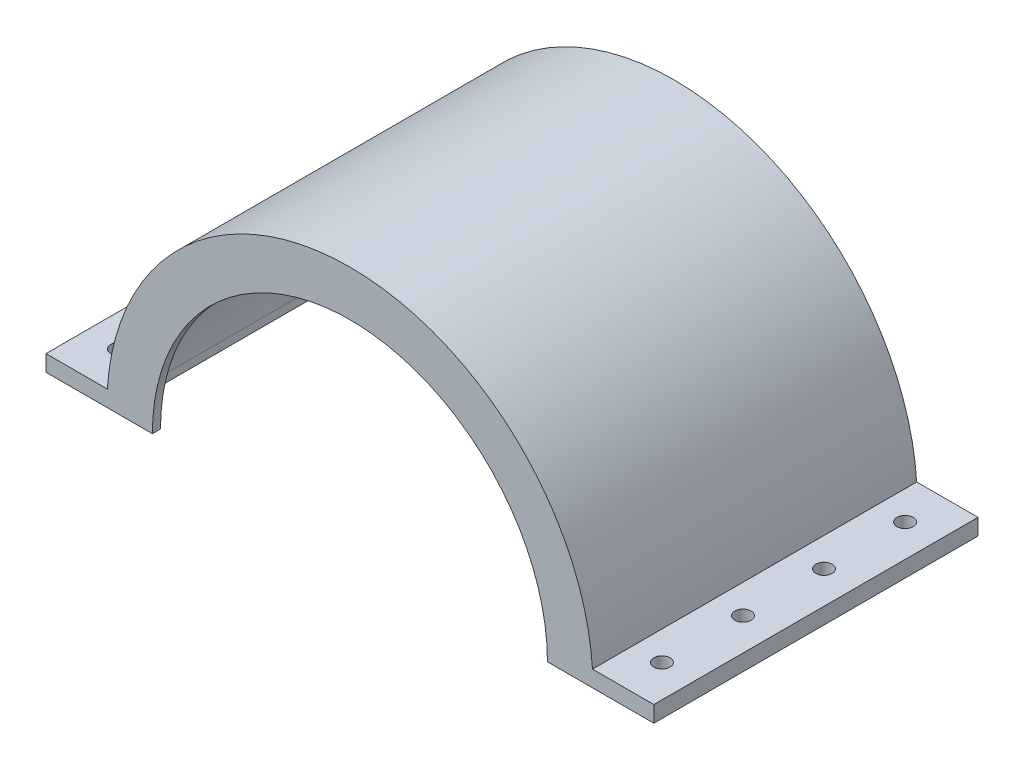
SolidWorks part; units mm, degrees
ref_plane "Front Plane" through (0, 0, 0) normal (0, 0, 1) x (1, 0, 0)
ref_plane "Top Plane" through (0, 0, 0) normal (0, 1, 0) x (1, 0, 0)
ref_plane "Right Plane" through (0, 0, 0) normal (1, 0, 0) x (0, 0, -1)
sketch "Sketch1" plane through (0, 0, 0) normal (0, 0, 1) x (1, 0, 0)
  line L0 (-75, 0) -> (75, 0)
  line L1 (0, 0) -> (0, 73.1042) construction
  line L2 (75, 0) -> (75, 4)
  line L3 (-75, 0) -> (-75, 4)
  line L4 (75, 4) -> (59.8665, 4)
  line L5 (-75, 4) -> (-59.8665, 4)
  arc A0 (59.8665, 4) -> (-59.8665, 4) centre (0, 0) ccw
  dimension "D1" = 120
  dimension "D2" = 75
  dimension "D3" = 73.1042
  dimension "D4" = 4
  dimension "D5" = 15.1335
extrude "Boss-Extrude1" add sketch "Sketch1" along normal blind 80
shell "Shell1" thickness 2
sketch "Sketch2" plane through (0, 2, 0) normal (0, -1, 0) x (1, 0, 0)
  line L1 (-73, 78) -> (-57.9655, 78)
  line L2 (-73, 78) -> (-73, 2)
  line L3 (-73, 2) -> (-57.9655, 2)
  line L4 (-57.9655, 78) -> (-57.9655, 2)
  line L5 (57.9123, 78) -> (73, 78)
  line L6 (57.9123, 78) -> (57.9123, 2)
  line L7 (57.9123, 2) -> (73, 2)
  line L8 (73, 78) -> (73, 2)
  dimension "D1" = 76
  dimension "D2" = 15.0345
  dimension "D3" = 76
  dimension "D4" = 15.0877
extrude "Boss-Extrude2" add sketch "Sketch2" along normal up to surface (2 mm away) up to face at (0, 0, 40)
sketch "Sketch3" plane through (0, 0, 80) normal (0, 0, 1) x (1, 0, 0)
  line L0 (-48.75, 0) -> (48.75, 0)
  arc A0 (48.75, 0) -> (-48.75, 0) centre (0, 0) ccw
  dimension "D2" = 97.5
extrude "Cut-Extrude1" cut sketch "Sketch3" against normal up to next
sketch "Sketch5" plane through (0, 0, 0) normal (0, 0, -1) x (-1, 0, 0)
  line L0 (-15, 0) -> (15, 0)
  arc A0 (15, 0) -> (-15, 0) centre (0, 0) ccw
  dimension "D1" = 30
  dimension "D2" = 30
extrude "Cut-Extrude2" cut sketch "Sketch5" against normal up to next
sketch "Sketch6" plane through (0, 0, 0) normal (0, -1, 0) x (1, 0, 0)
  circle A0 centre (67, 70) radius 2
  dimension "D3" = 4
  dimension "D4" = 67
  dimension "D5" = 70
extrude "Cut-Extrude6" cut sketch "Sketch6" against normal through all
pattern_linear "LPattern1" count 4 spacing 20 along (0, 0, -1) of "Cut-Extrude6"
ref_plane "Plane1" through (0, 0, 0) normal (1, 0, 0) x (0, 0, -1)
mirror "Mirror1" about plane through (0, 0, 0) normal (1, 0, 0) of "LPattern1", "Cut-Extrude6"
ref_plane "Plane2" through (-81.5, 0, 0) normal (1, 0, 0) x (0, 0, -1)
ref_plane "Plane3" through (0, 0, 40) normal (0, 0, 1) x (1, 0, 0)
sketch "Sketch7" plane through (0, 0, 40) normal (0, 0, 1) x (1, 0, 0)
  line L0 (-81.5, -45.1099) -> (-81.5, 45.1099) construction
  line L1 (-39.911, -2.6667) -> (-39.911, 97.3333) construction
  line L3 (59.8665, 4) -> (-39.911, -2.6667) construction
  line L4 (-39.911, 97.3333) -> (-81.5, 97.3333)
  arc A0 (59.8665, 4) -> (-39.911, 97.3333) centre (-39.911, -2.6667) ccw
  point P8 (-81.5, 0)
  point P9 (-81.5, 137.1762)
  dimension "D3" = 100
  dimension "D1" = 97.3333
sketch "Sketch11" plane through (-81.5, 0, 0) normal (1, 0, 0) x (0, 0, -1)
  line L0 (-225.3158, 127.91) -> (-214.0658, 106.91) construction
  line L1 (-225.3158, 127.91) -> (-202.8158, 127.91)
  line L2 (-240.3158, 112.91) -> (-240.3158, 100.91)
  line L3 (-225.3158, 85.91) -> (-202.8158, 85.91)
  line L4 (-187.8158, 112.91) -> (-187.8158, 100.91)
  line L5 (-214.0658, 106.91) -> (-202.8158, 85.91) construction
  line L6 (-225.3158, 85.91) -> (-202.8158, 127.91) construction
  arc A0 (-202.8158, 85.91) -> (-187.8158, 100.91) centre (-202.8158, 100.91) ccw
  arc A1 (-225.3158, 85.91) -> (-240.3158, 100.91) centre (-225.3158, 100.91) cw
  arc A2 (-225.3158, 127.91) -> (-240.3158, 112.91) centre (-225.3158, 112.91) ccw
  arc A3 (-202.8158, 127.91) -> (-187.8158, 112.91) centre (-202.8158, 112.91) cw
  dimension "D3" = 15
  dimension "D1" = 42
  dimension "D2" = 52.5
sketch "Sketch12" plane through (0, 0, 40) normal (0, 0, 1) x (1, 0, 0)
  line L0 (-81.5, 55.5522) -> (0, 55.5522)
